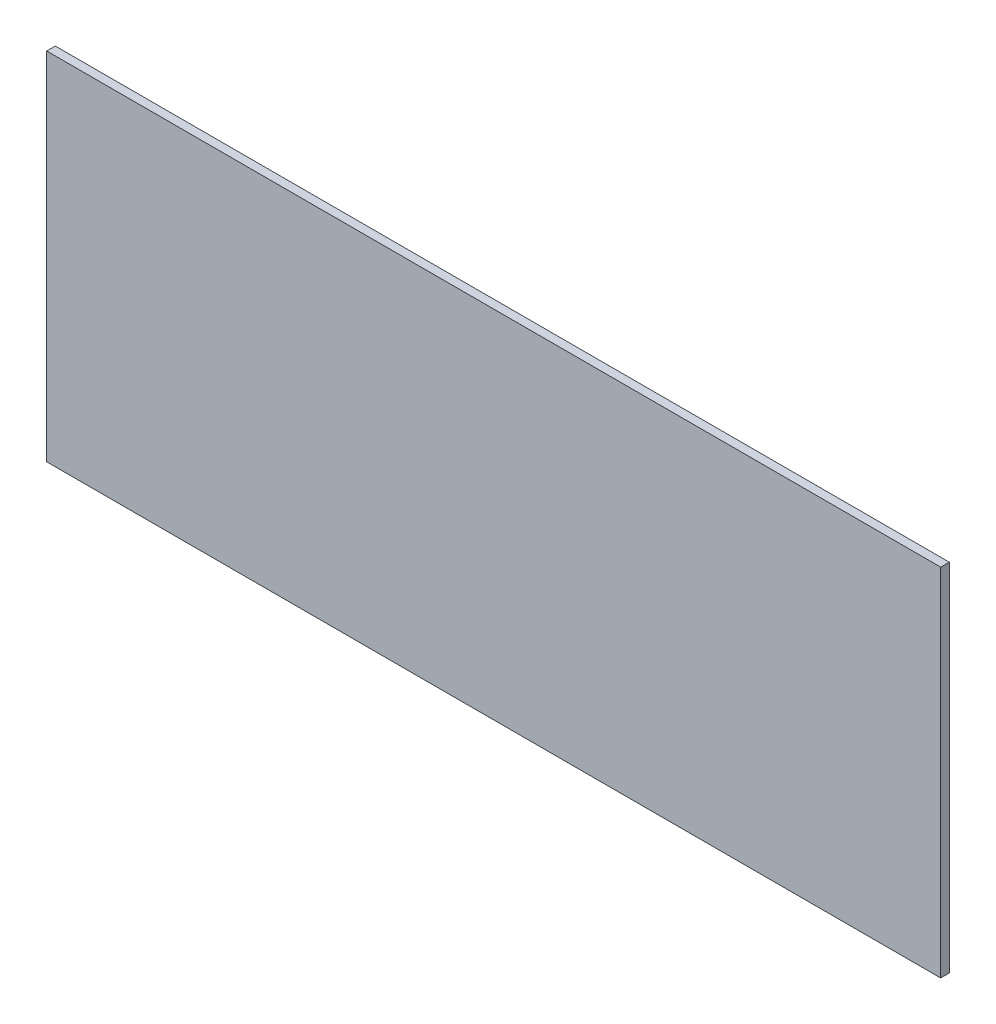
SolidWorks part; units mm, degrees
ref_plane "Front Plane" through (0, 0, 0) normal (0, 0, 1) x (1, 0, 0)
ref_plane "Top Plane" through (0, 0, 0) normal (0, 1, 0) x (1, 0, 0)
ref_plane "Right Plane" through (0, 0, 0) normal (1, 0, 0) x (0, 0, -1)
sketch "Sketch1" plane through (0, 0, 0) normal (0, 0, 1) x (1, 0, 0)
  line L4 (104, 47.8533) -> (-104, 47.8533)
  line L5 (104, -34.9295) -> (104, 47.8533)
  line L6 (-104, -34.9295) -> (104, -34.9295)
  line L7 (-104, 47.8533) -> (-104, -34.9295)
  line L8 (104, 47.8533) -> (-104, 47.8533)
  line L9 (104, -34.9295) -> (104, 47.8533)
  line L10 (-104, -34.9295) -> (104, -34.9295)
  line L11 (-104, 47.8533) -> (-104, -34.9295)
  dimension "D1" = 0
extrude "Boss-Extrude1" add sketch "Sketch1" against normal blind 2
